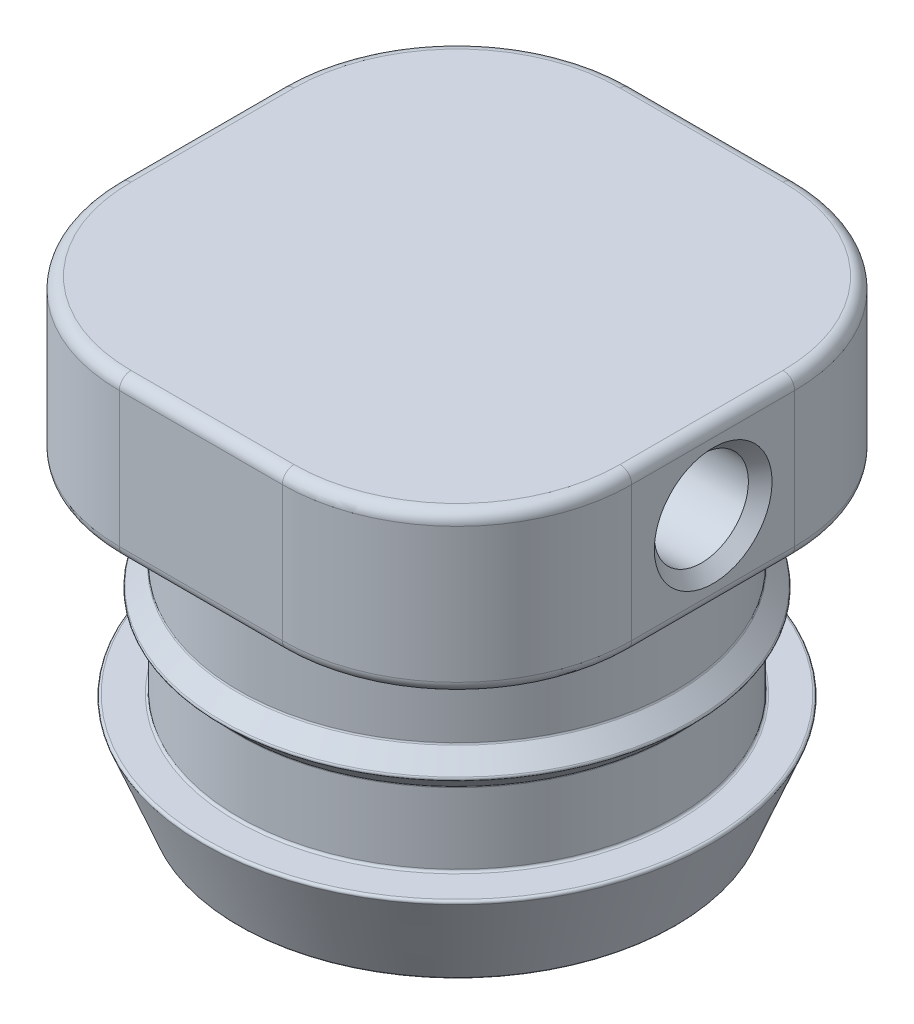
SolidWorks part; units mm, degrees
ref_plane "Front Plane" through (0, 0, 0) normal (0, 0, 1) x (1, 0, 0)
ref_plane "Top Plane" through (0, 0, 0) normal (0, 1, 0) x (1, 0, 0)
ref_plane "Right Plane" through (0, 0, 0) normal (1, 0, 0) x (0, 0, -1)
sketch "Sketch1" plane through (0, 0, 0) normal (0, 0, 1) x (1, 0, 0)
  line L3 (0, 0) -> (0, -6.8) construction
  line L4 (-11, 0) -> (0, 0)
  line L5 (-11, 0) -> (-11, -6.8)
  line L6 (-11, -6.8) -> (11, -6.8)
  line L7 (11, 0) -> (11, -6.8)
  line L8 (0, 0) -> (11, 0)
  point P1 (-0.2751, 0)
  point P4 (0.2751, 0)
  dimension "D4" = 22
  dimension "D5" = 6.8
extrude "Boss-Extrude1" add sketch "Sketch1" along normal mid plane 22
sketch3d "3DSketch1" plane through (0, 0, 0) normal (0, 0, 1) x (1, 0, 0)
  dimension "D1" = 12.7
sketch "Sketch2" plane through (0, 0, 0) normal (0, 0, 1) x (1, 0, 0)
  line L0 (0, 9.544) -> (0, -9.544) construction
  line L1 (0, -6.8) -> (9.365, -6.8)
  line L4 (0, -19.5) -> (9.365, -19.5)
  line L10 (0, -19.5) -> (0, -6.8)
  line L11 (9.365, -19.5) -> (10.9525, -15.5312)
  line L12 (10.9525, -15.5312) -> (9.365, -15.5312)
  line L13 (9.365, -15.5312) -> (9.365, -12.3562)
  line L14 (9.365, -12.3562) -> (10.1588, -11.5625)
  line L15 (10.1588, -11.5625) -> (9.365, -10.7688)
  line L16 (10.1588, -11.5625) -> (9.365, -11.5625) construction
  line L17 (9.365, -10.7688) -> (9.365, -6.8)
  dimension "D1" = 18.73
  dimension "D2" = 12.7
  dimension "D3" = 1.5875
  dimension "D4" = 3.9688
  dimension "D5" = 0.7937
  dimension "D6" = 7.9375
  dimension "D7" = 6.8
revolve "Revolve1" add sketch "Sketch2" angle 360 about L0
sketch "Sketch3" plane through (0, -19.5, 0) normal (0, -1, 0) x (1, 0, 0)
  circle A0 centre (0, 0) radius 4
  dimension "D1" = 8
extrude "Cut-Extrude1" cut sketch "Sketch3" against normal blind 18.5 contours A0
hole_wizard "#10-32 Tapped Hole1" positions "Sketch4" profile "Sketch5" tap size "#10-32" standard "ANSI Inch"
sketch "Sketch4" plane through (11, 0, 0) normal (1, 0, 0) x (0, 0, -1)
  point P0 (0, -3.4)
  dimension "D1" = 3.4
cosmetic thread "Hole Thread1" parameters "D2"=4.826
sketch "Sketch5" plane through (11, -3.4, 0) normal (0, 1, 0) x (0, 0, -1)
  line L0 (0, 0) -> (0, 7)
  line L1 (0, 7) -> (2.0193, 7)
  line L2 (2.0193, 7) -> (2.0193, 0)
  line L5 (2.0193, 0) -> (0, 0)
  line L11 (0, -6.35) -> (0, 107.95) construction
  dimension "Thru Tap Drill Dia." = 4.0386
  dimension "Thru Tap Drill Depth" = 7
fillet "Fillet3" radius 0.1 8 edges at (-10.9525, -15.5313, 0) (-10.1587, -11.5625, 0) (4, -1, 0) (-9.365, -19.5, 0) (-9.365, -6.8, 0) (-9.365, -10.7688, 0) (-9.365, -12.3563, 0) (-9.365, -15.5313, 0)
chamfer "Chamfer1" distance 0.508 angle 45 1 edges at (11, -3.4, -2.0193)
fillet "Fillet6" radius 7.5 4 edges at (11, -3.4, -11) (-11, -3.4, -11) (-11, -3.4, 11) (11, -3.4, 11)
fillet "Fillet8" radius 0.5 18 edges at (-8.8033, -6.8, 8.8033) (-11, -6.8, 0) (-8.8033, -6.8, -8.8033) (0, -6.8, -11) (8.8033, -6.8, -8.8033) (11, -6.8, 0) (8.8033, -6.8, 8.8033) (8.8033, 0, 8.8033) (-8.8033, 0, 8.8033) (-11, 0, 0) (-8.8033, 0, -8.8033) (8.8033, 0, -8.8033) (0, -6.8, 11) (11, 0, 0) (0, 0, 11) (0, 0, -11) (3.995, -5.4095, -0.1991) (4, -19.5, 0)
